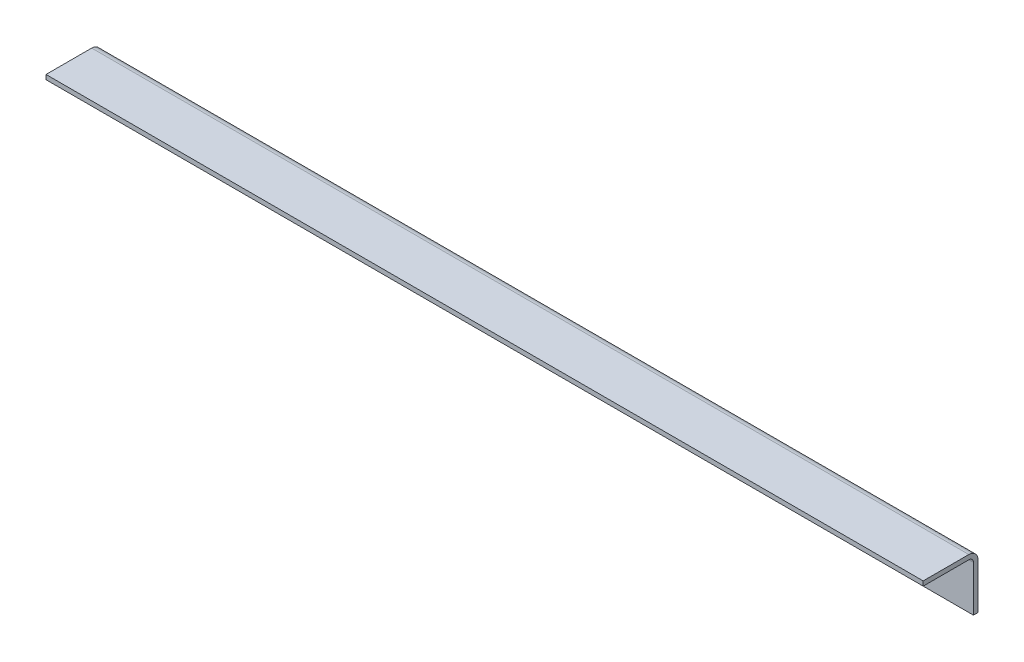
SolidWorks part; units mm, degrees
ref_plane "Front Plane" through (0, 0, 0) normal (0, 0, 1) x (1, 0, 0)
ref_plane "Top Plane" through (0, 0, 0) normal (0, 1, 0) x (1, 0, 0)
ref_plane "Right Plane" through (0, 0, 0) normal (1, 0, 0) x (0, 0, -1)
sketch "Sketch2" plane through (0, 0, 0) normal (1, 0, 0) x (0, 0, -1)
  line L0 (-38.1, 0) -> (0, 0)
  line L1 (0, 0) -> (0, -38.1)
  line L2 (0, -38.1) -> (-3.175, -38.1)
  line L3 (-3.175, -38.1) -> (-3.175, -3.175)
  line L4 (-3.175, -3.175) -> (-38.1, -3.175)
  line L5 (-38.1, -3.175) -> (-38.1, 0)
  dimension "D1" = 38.1
  dimension "D2" = 3.175
extrude "Boss-Extrude1" add sketch "Sketch2" along normal blind 609.6
fillet "Fillet1" radius 3.175 1 edges at (304.8, -3.175, 3.175)
fillet "Fillet2" radius 6.35 1 edges at (304.8, 0, 0)
sketch "Sketch3" plane through (0, 0, 3.175) normal (0, 0, 1) x (1, 0, 0)
  line L0 (609.6, 0) -> (0, 0) construction
  line L1 (609.6, -6.35) -> (609.6, -38.1) construction
  line L2 (0, -6.35) -> (0, -38.1) construction
  line L3 (0, -3.175) -> (609.6, -3.175) construction
  circle A0 centre (304.8, -22.225) radius 3.3782
  circle A1 centre (558.8, -22.225) radius 3.3782
  circle A2 centre (50.8, -22.225) radius 3.3782
  point P6 (0, 0)
  point P11 (29.3833, -22.225)
  point P14 (0, 0)
  point P17 (304.8, -3.175)
  dimension "D1" = 22.225
  dimension "D2" = 6.7564
  dimension "D3" = 50.8
  dimension "D4" = 50.8
extrude "Cut-Extrude1" cut sketch "Sketch3" against normal through all
